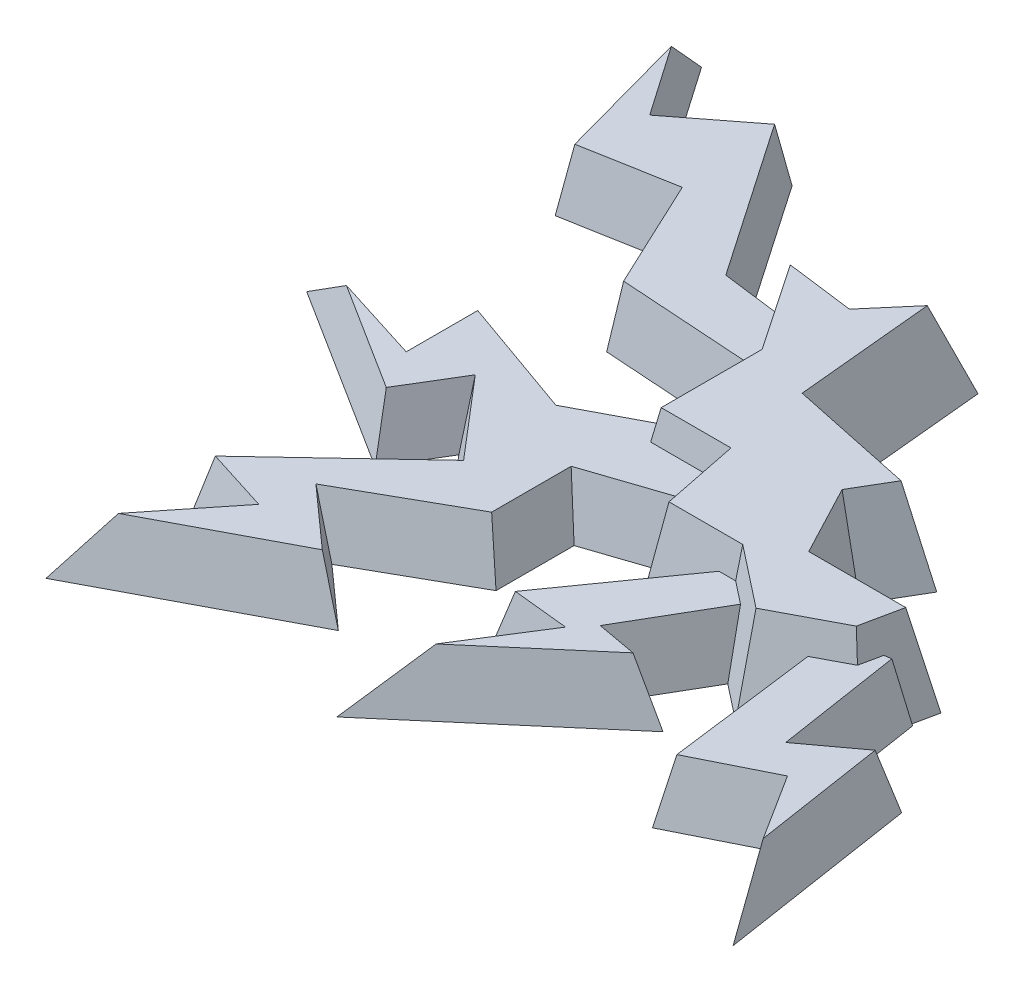
SolidWorks part; units mm, degrees
material "ABS"
ref_plane "Front Plane" through (0, 0, 0) normal (0, 0, 1) x (1, 0, 0)
ref_plane "Top Plane" through (0, 0, 0) normal (0, 1, 0) x (1, 0, 0)
ref_plane "Right Plane" through (0, 0, 0) normal (1, 0, 0) x (0, 0, -1)
sketch "Sketch1" plane through (0, 0, 0) normal (0, 1, 0) x (1, 0, 0)
  line L1 (-17.5, 17.5) -> (17.5, 17.5)
  line L2 (-17.5, 17.5) -> (-17.5, -17.5)
  line L3 (-17.5, -17.5) -> (17.5, -17.5)
  line L4 (17.5, 17.5) -> (17.5, -17.5)
  line L5 (-17.5, 17.5) -> (17.5, -17.5) construction
  line L6 (-17.5, -17.5) -> (17.5, 17.5) construction
  point P0 (0, 0)
  dimension "D1" = 35
sketch "Sketch2" plane through (0, 0, 0) normal (0, 1, 0) x (1, 0, 0)
  line L0 (-1.5283, 5.4924) -> (-1.003, 0)
  line L1 (-1.003, 0) -> (3.5342, -0.9552)
  line L2 (3.5342, -0.9552) -> (2.579, -2.579)
  line L3 (-17.5, 17.5) -> (17.5, -17.5) construction
  line L4 (2.579, -2.579) -> (3.5342, -4.3939)
  line L5 (3.5342, -4.3939) -> (7.1163, -4.3939)
  line L6 (7.1163, -4.3939) -> (6.6428, -6.6428)
  line L7 (6.6428, -6.6428) -> (3.917, -8.0775)
  line L8 (3.917, -8.0775) -> (1.7194, -6.3521)
  line L9 (1.7194, -6.3521) -> (-1.003, -6.3521)
  line L10 (-1.003, -6.3521) -> (-1.5283, -3.7483)
  line L11 (-1.5283, -3.7483) -> (-3.9641, -3.7483)
  line L12 (-3.9641, -3.7483) -> (-3.9641, 0)
  line L13 (-3.9641, 0) -> (-6.5073, 3.7611)
  line L14 (-6.5073, 3.7611) -> (-3.3551, 3.3551)
  line L15 (-3.3551, 3.3551) -> (-1.5283, 5.4924)
  point P2 (0, 0)
  point P18 (-3.9641, 0)
extrude "Boss-Extrude1" add sketch "Sketch2" along normal blind 3 draft 10
sketch "Sketch3" plane through (0, 0, 0) normal (0, 1, 0) x (1, 0, 0)
  line L0 (10.387, -14.6309) -> (9.3544, -7.9486)
  line L1 (9.3544, -7.9486) -> (7.6303, -9.2212)
  line L2 (7.6303, -9.2212) -> (7.0153, -5.2413)
  line L3 (7.0153, -5.2413) -> (4.7089, -5.5977)
  line L4 (4.7089, -5.5977) -> (5.6137, -12.5622)
  line L5 (5.6137, -12.5622) -> (8.2458, -11.2513)
  line L6 (8.2458, -11.2513) -> (10.387, -14.6309)
  line L7 (3.7074, -5.391) -> (1.4272, -9.3077)
  line L8 (1.4272, -9.3077) -> (3.0034, -9.5963)
  line L9 (3.0034, -9.5963) -> (-2.8914, -14.6309)
  line L10 (-2.8914, -14.6309) -> (-0.27, -10.4836)
  line L11 (-0.27, -10.4836) -> (-2.1808, -10.2851)
  line L12 (-2.1808, -10.2851) -> (1.989, -4.3906)
  line L13 (1.989, -4.3906) -> (3.7074, -5.391)
  line L14 (-11.7893, -15.4832) -> (-5.3747, -12.0994)
  line L15 (-5.3747, -12.0994) -> (-7.4047, -10.2851)
  line L16 (-7.4047, -10.2851) -> (-3.89, -8.2994)
  line L17 (-3.89, -8.2994) -> (-3.89, -5.6824)
  line L18 (-3.89, -5.6824) -> (1.091, -4.0116)
  line L19 (1.091, -4.0116) -> (-0.8152, -0.6375)
  line L20 (-0.8152, -0.6375) -> (-6.297, -3.5292)
  line L22 (-6.297, -3.5292) -> (-10.6806, -1.9759)
  line L23 (-10.6806, -1.9759) -> (-10.6806, -4.3906)
  line L24 (-10.6806, -4.3906) -> (-15.7429, -2.7919)
  line L25 (-15.7429, -2.7919) -> (-9.5118, -6.7303)
  line L26 (-9.5118, -6.7303) -> (-8.4553, -4.9812)
  line L27 (-8.4553, -4.9812) -> (-6.7016, -7.0345)
  line L28 (-6.7016, -7.0345) -> (-11.18, -11.2513)
  line L29 (-11.18, -11.2513) -> (-8.9677, -11.95)
  line L30 (-8.9677, -11.95) -> (-11.7893, -15.4832)
  line L31 (-15.64, 10.3384) -> (-13.7824, 3.5755)
  line L32 (-13.7824, 3.5755) -> (-10.6806, 4.1346)
  line L33 (-10.6806, 4.1346) -> (-8.9677, 0.4859)
  line L34 (-8.9677, 0.4859) -> (-1.6605, 0)
  line L35 (-1.6605, 0) -> (-3.9653, 2.6535)
  line L36 (-3.9653, 2.6535) -> (-6.9953, 3.0385)
  line L37 (-6.9953, 3.0385) -> (-10.6806, 8.4139)
  line L38 (-10.6806, 8.4139) -> (-13.0401, 6.5864)
  line L39 (-13.0401, 6.5864) -> (-15.64, 10.3384)
  point P23 (-8.9677, -4.9812)
  point P33 (-10.6806, -4.3906)
  point P41 (0, 0)
  point P42 (-6.0777, -4.6098)
  point P43 (-5.5403, -3.7974)
  point P44 (-8.4553, -4.9812)
  point P45 (-6.297, -12.6099)
  point P46 (-7.6871, -10.0327)
  point P47 (-3.89, -8.2994)
  point P48 (-2.2263, -10.2851)
  point P49 (-1.6605, -9.5963)
  point P50 (0, 0)
  point P51 (-0.27, -10.4836)
  point P52 (0, 0)
  point P53 (-10.6806, 4.1346)
  point P54 (-1.6605, 0)
  point P55 (7.0703, -9.3077)
  point P56 (4.7089, -11.2513)
  point P57 (9.8356, -10.4836)
  point P58 (7.4064, -11.2513)
  point P59 (5.4748, -10.9183)
  point P60 (1.4272, -9.3077)
  point P61 (-2.1808, -10.4836)
  point P62 (5.6137, -12.5622)
  point P63 (9.6771, -8.942)
  point P64 (10.387, -14.6309)
  point P65 (8.2458, -11.2513)
  point P66 (9.3544, -7.9486)
extrude "Boss-Extrude2" add sketch "Sketch3" along normal blind 2 draft 10
